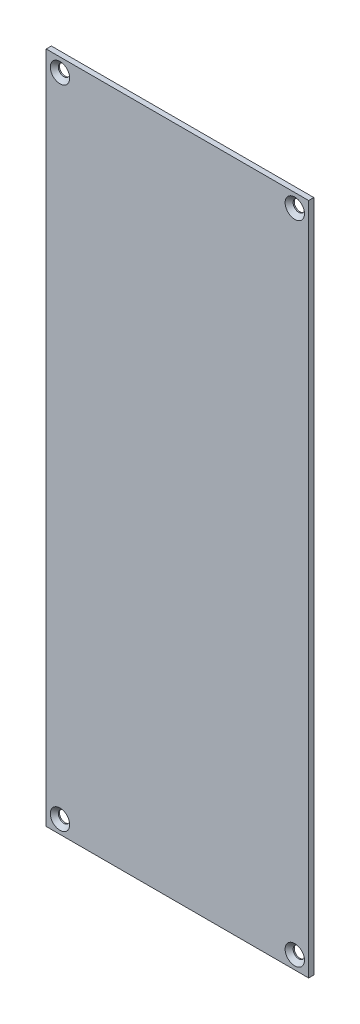
SolidWorks part; units mm, degrees
ref_plane "Front Plane" through (0, 0, 0) normal (0, 0, 1) x (1, 0, 0)
ref_plane "Top Plane" through (0, 0, 0) normal (0, 1, 0) x (1, 0, 0)
ref_plane "Right Plane" through (0, 0, 0) normal (1, 0, 0) x (0, 0, -1)
sketch "Sketch1" plane through (0, 0, 0) normal (0, 0, 1) x (1, 0, 0)
  line L0 (0, 130.33) -> (0, 0)
  line L1 (50.8, 130.33) -> (0, 130.33)
  line L2 (50.8, 0) -> (50.8, 130.33)
  line L3 (0, 0) -> (50.8, 0)
  dimension "D1" = 50.8
  dimension "D2" = 130.33
extrude "Boss-Extrude1" add sketch "Sketch1" along normal blind 1
hole_wizard "CSK for M2 Flat Head Machine Screw1" positions "Sketch6" profile "Sketch4" countersink size "M2" standard "ANSI Metric" end condition up to next
sketch "Sketch6" plane through (0, 0, 1) normal (0, 0, 1) x (1, 0, 0)
  line L2 (2.6725, 127.7025) -> (48.1225, 127.7025) construction
  line L3 (48.1225, 127.7025) -> (48.1225, 2.5625) construction
  line L4 (48.1225, 2.5625) -> (2.6725, 2.5625) construction
  line L5 (2.6725, 2.5625) -> (2.6725, 127.7025) construction
  line L16 (50.8, 130.33) -> (0, 130.33) construction
  line L17 (0, 130.33) -> (0, 0) construction
  point P3 (48.1225, 127.7025)
  point P6 (2.6725, 2.5625)
  point P9 (48.1225, 2.5625)
  point P15 (2.6725, 127.7025)
  dimension "D1" = 2.6275
  dimension "D2" = 2.6725
  dimension "D3" = 45.45
  dimension "D4" = 125.14
sketch "Sketch4" plane through (48.1225, 127.7025, 1) normal (1, 0, 0) x (0, -1, 0)
  line L0 (0, 0) -> (0, 1)
  line L1 (0, 1) -> (1.1, 1)
  line L2 (1.1, 1) -> (1.1, 0.775)
  line L3 (1.1, 0.775) -> (1.875, 0)
  line L5 (1.875, 0) -> (0, 0)
  line L6 (-1.1, 0.775) -> (-1.875, 0) construction
  line L11 (0, -6.35) -> (0, 107.95) construction
  dimension "Thru Hole Dia." = 2.2
  dimension "Thru Hole Depth" = 1
  dimension "Near C'Sink Dia." = 3.75
  dimension "Near C'Sink Angle" = 90
